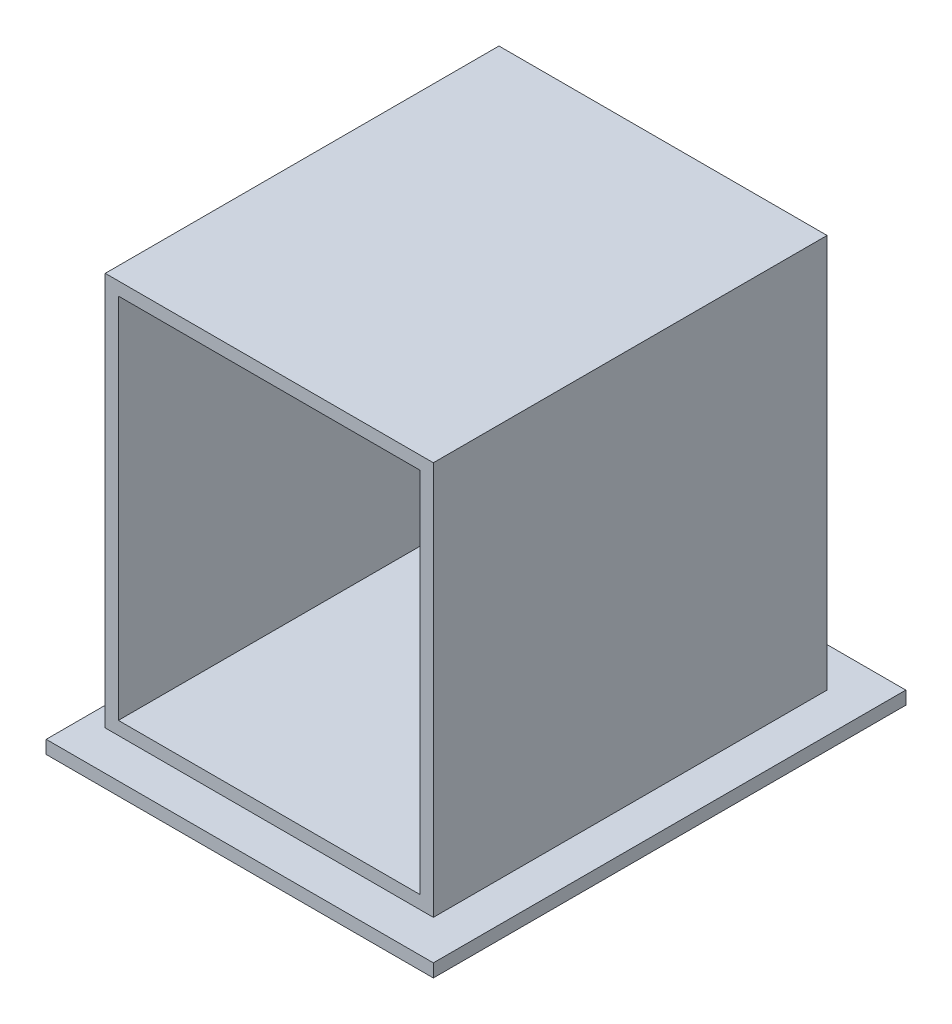
SolidWorks part; units mm, degrees
ref_plane "前视基准面" through (0, 0, 0) normal (0, 0, 1) x (1, 0, 0)
ref_plane "上视基准面" through (0, 0, 0) normal (0, 1, 0) x (1, 0, 0)
ref_plane "右视基准面" through (0, 0, 0) normal (1, 0, 0) x (0, 0, -1)
sketch "草图1" plane through (0, 0, 0) normal (0, 0, 1) x (1, 0, 0)
  line L1 (0, 0) -> (250, 0)
  line L2 (0, 0) -> (0, 300)
  line L3 (0, 300) -> (250, 300)
  line L4 (250, 0) -> (250, 300)
  dimension "D1" = 250
  dimension "D2" = 300
extrude "凸台-拉伸1" add sketch "草图1" along normal blind 300
sketch "草图2" plane through (0, 0, 300) normal (0, 0, 1) x (1, 0, 0)
  line L0 (250, 0) -> (250, 300) construction
  line L1 (10, 10) -> (240, 10)
  line L2 (10, 10) -> (10, 290)
  line L3 (10, 290) -> (240, 290)
  line L4 (240, 10) -> (240, 290)
  line L5 (250, 300) -> (0, 300) construction
  line L6 (0, 300) -> (0, 0) construction
  line L7 (0, 0) -> (250, 0) construction
  dimension "D1" = 10
  dimension "D2" = 10
  dimension "D3" = 10
  dimension "D4" = 10
extrude "切除-拉伸1" cut sketch "草图2" against normal blind 290
sketch "草图3" plane through (0, 0, 0) normal (0, -1, 0) x (1, 0, 0)
  line L0 (250, 300) -> (250, 0) construction
  line L1 (-15, 330) -> (280, 330)
  line L2 (-15, 330) -> (-15, -30)
  line L3 (-15, -30) -> (280, -30)
  line L4 (280, 330) -> (280, -30)
  line L5 (0, 300) -> (0, 0) construction
  line L6 (0, 300) -> (250, 300) construction
  line L7 (0, 0) -> (250, 0) construction
  dimension "D1" = 30
  dimension "D2" = 15
  dimension "D3" = 30
  dimension "D4" = 30
extrude "凸台-拉伸2" add sketch "草图3" along normal blind 10
sketch "草图4" plane through (0, -10, 0) normal (0, -1, 0) x (-1, 0, 0)
  line L0 (-101.8115, -270) -> (-183.6499, -270) construction
  line L1 (-101.8115, -287.7381) -> (-183.6499, -287.7381)
  line L2 (-101.8115, -252.2619) -> (-183.6499, -252.2619)
  line L3 (-280, -330) -> (15, -330) construction
  arc A0 (-101.8115, -287.7381) -> (-101.8115, -252.2619) centre (-101.8115, -270) ccw
  arc A1 (-183.6499, -252.2619) -> (-183.6499, -287.7381) centre (-183.6499, -270) ccw
  point P2 (-142.7307, -270)
  dimension "D1" = 60
extrude "切除-拉伸2" cut sketch "草图4" against normal blind 10
